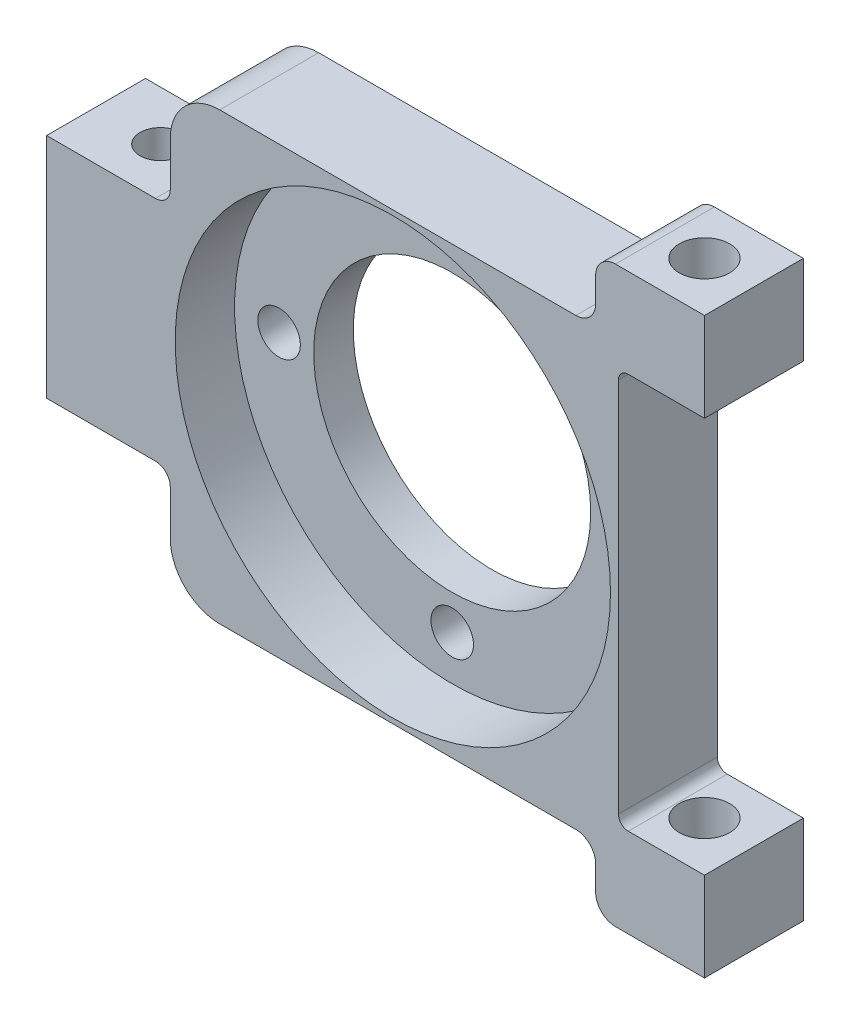
SolidWorks part; units mm, degrees
material "1060 合金"
ref_plane "前视基准面" through (0, 0, 0) normal (0, 0, 1) x (1, 0, 0)
ref_plane "上视基准面" through (0, 0, 0) normal (0, 1, 0) x (1, 0, 0)
ref_plane "右视基准面" through (0, 0, 0) normal (1, 0, 0) x (0, 0, -1)
sketch "草图1" plane through (0, 0, 0) normal (0, 0, 1) x (1, 0, 0)
  line L0 (0, 0) -> (17.5, 0) construction
  line L1 (0, 0) -> (0, 17.5) construction
  line L3 (-35, 29) -> (35, 29)
  line L4 (-35, 29) -> (-35, -29)
  line L5 (-35, -29) -> (35, -29)
  line L6 (35, 29) -> (35, -29)
  line L7 (-35, 29) -> (35, -29) construction
  line L8 (-35, -29) -> (35, 29) construction
  circle A0 centre (0, 0) radius 17.5 construction
  circle A1 centre (17.5, 0) radius 2.15
  circle A2 centre (0, -17.5) radius 2.15
  circle A3 centre (-17.5, 0) radius 2.15
  circle A4 centre (0, 17.5) radius 2.15
  circle A5 centre (0, 0) radius 14
  dimension "D1" = 35
  dimension "D2" = 4.3
  dimension "D4" = 28
  dimension "D5" = 58
  dimension "D6" = 70
  dimension "D3" = 4
extrude "凸台-拉伸1" add sketch "草图1" along normal blind 10
sketch "草图2" plane through (0, 0, 10) normal (0, 0, 1) x (1, 0, 0)
  circle A0 centre (0, 0) radius 22
  dimension "D1" = 44
extrude "切除-拉伸1" cut sketch "草图2" against normal blind 6
sketch "草图3" plane through (0, 29, 0) normal (0, 1, 0) x (1, 0, 0)
  line L0 (35, -5) -> (26.5, -5) construction
  line L1 (35, -10) -> (35, 0) construction
  circle A0 centre (26.5, -5) radius 2.55
  dimension "D1" = 5.1
  dimension "D2" = 8.5
extrude "切除-拉伸2" cut sketch "草图3" against normal through all both and the other way through all
sketch "草图4" plane through (0, 29, 0) normal (0, 1, 0) x (1, 0, 0)
  line L0 (26.5, -5) -> (-28.5, -5) construction
  circle A0 centre (-28.5, -5) radius 2.05
  dimension "D1" = 55
  dimension "D2" = 4.1
extrude "切除-拉伸3" cut sketch "草图4" against normal through all both and the other way through all
sketch "草图6" plane through (0, 0, 0) normal (0, 0, -1) x (-1, 0, 0)
  line L0 (0, 0) -> (35, 0) construction
  line L1 (35, 29) -> (35, -29) construction
  line L2 (22.5, 29) -> (22.5, 11.5)
  line L3 (-35, 29) -> (35, 29) construction
  line L4 (22.5, 11.5) -> (35, 11.5)
  line L5 (35, 11.5) -> (35, 29)
  line L6 (35, 29) -> (22.5, 29)
  line L11 (30.55, -29) -> (26.45, -29) construction
  line L12 (28.5, -29) -> (28.5, 29) construction
  line L13 (35, -29) -> (22.5, -29)
  line L14 (35, -11.5) -> (35, -29)
  line L15 (22.5, -11.5) -> (35, -11.5)
  line L16 (22.5, -29) -> (22.5, -11.5)
  dimension "D1" = 17.5
  dimension "D2" = 6
extrude "切除-拉伸4" cut sketch "草图6" against normal through all
fillet "圆角1" radius 1.5 2 edges at (-22.5, -11.5, 5) (-22.5, 11.5, 5)
sketch "草图7" plane through (0, 29, 0) normal (0, 1, 0) x (1, 0, 0)
  line L0 (31.5, 0) -> (31.5, -10)
  line L1 (35, -10) -> (-22.5, -10) construction
  line L2 (31.5, -10) -> (35, -10)
  line L3 (35, -10) -> (35, 0)
  line L4 (35, 0) -> (31.5, 0)
  circle A0 centre (26.5, -5) radius 2.55 construction
  dimension "D1" = 5
extrude "切除-拉伸5" cut sketch "草图7" against normal through all both and the other way through all
fillet "圆角2" [suppressed] radius 10
sketch "草图8" plane through (0, 0, 10) normal (0, 0, 1) x (1, 0, 0)
  line L0 (0, 0) -> (31.5, 0) construction
  line L1 (31.5, -29) -> (31.5, 29) construction
  line L2 (31.5, 20) -> (31.5, -20)
  line L3 (31.5, -20) -> (22.8, -20)
  line L4 (22.8, -20) -> (22.8, 20)
  line L5 (-22.5, -29) -> (31.5, -29) construction
  line L6 (31.5, 20) -> (22.8, 20)
  line L7 (23.95, -29) -> (29.05, -29) construction
  line L8 (26.5, -29) -> (26.5, 0) construction
  point P12 (22.8, 0)
  dimension "D1" = 3.7
  dimension "D2" = 9
extrude "切除-拉伸6" cut sketch "草图8" against normal through all
fillet "圆角3" radius 1 2 edges at (22.8, -20, 5) (22.8, 20, 5)
sketch "草图9" plane through (0, 0, 10) normal (0, 0, 1) x (1, 0, 0)
  line L0 (0, 0) -> (38.6255, 0) construction
  line L1 (-22.5, -22.5) -> (20.5, -22.5)
  line L2 (-22.5, -13) -> (-22.5, -29) construction
  line L3 (20.5, -22.5) -> (20.5, -29)
  line L4 (-22.5, -29) -> (31.5, -29) construction
  line L5 (20.5, -29) -> (-22.5, -29)
  line L6 (-22.5, -29) -> (-22.5, -22.5)
  line L7 (20.5, 29) -> (-22.5, 29)
  line L8 (20.5, 22.5) -> (20.5, 29)
  line L9 (-22.5, 22.5) -> (20.5, 22.5)
  line L10 (-22.5, 29) -> (-22.5, 22.5)
  dimension "D1" = 6.5
  dimension "D2" = 43
extrude "切除-拉伸7" cut sketch "草图9" against normal through all
fillet "圆角4" radius 5 2 edges at (-22.5, 22.5, 5) (-22.5, -22.5, 5)
fillet "圆角5" radius 2 4 edges at (20.5, 29, 5) (20.5, 22.5, 5) (20.5, -22.5, 5) (20.5, -29, 5)
